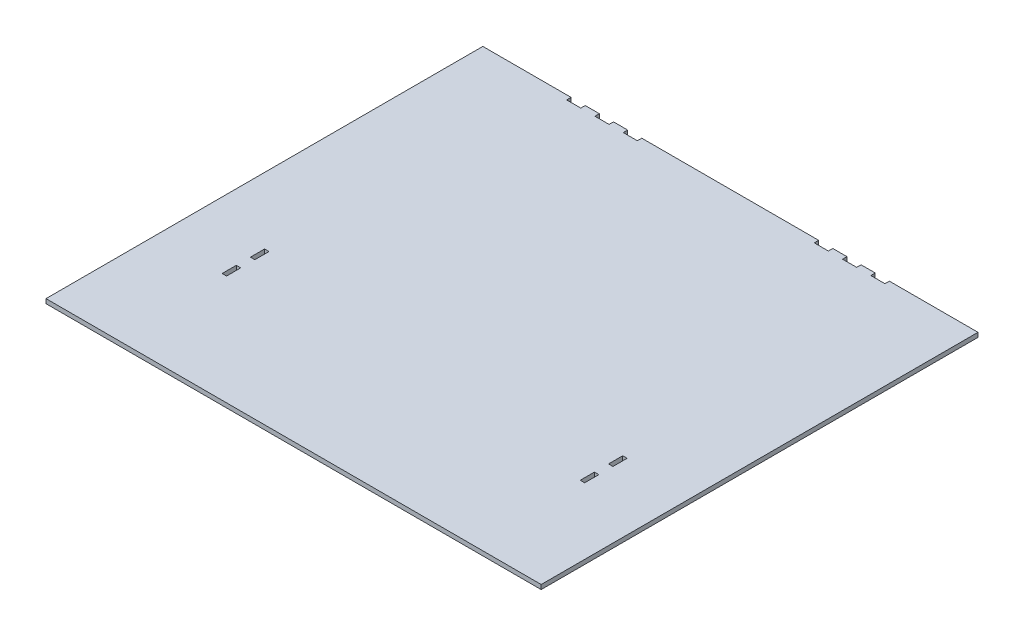
SolidWorks part; units mm, degrees
ref_plane "Front Plane" through (0, 0, 0) normal (0, 0, 1) x (1, 0, 0)
ref_plane "Top Plane" through (0, 0, 0) normal (0, 1, 0) x (1, 0, 0)
ref_plane "Right Plane" through (0, 0, 0) normal (1, 0, 0) x (0, 0, -1)
sketch "Sketch1" plane through (0, 0, 0) normal (0, 1, 0) x (1, 0, 0)
  line L1 (-280, 247) -> (-180.2136, 247)
  line L2 (-280, 247) -> (-280, -247)
  line L3 (-280, -247) -> (280, -247)
  line L4 (280, 247) -> (280, -247)
  line L5 (-280, 247) -> (280, -247) construction
  line L6 (-280, -247) -> (280, 247) construction
  line L8 (-200, -74.801) -> (-200, -90.8019)
  line L11 (-100.2136, 247) -> (99.7864, 247)
  line L12 (-100.2136, 242) -> (-116.2136, 242)
  line L14 (-180.2136, 242) -> (-180.2136, 247)
  line L20 (-100.2136, 242) -> (-100.2136, 247)
  line L21 (-132.2136, 242) -> (-148.2136, 242)
  line L23 (-132.2136, 247) -> (-116.2136, 247)
  line L29 (-164.2136, 242) -> (-180.2136, 242)
  line L30 (-164.2136, 242) -> (-164.2136, 247)
  line L31 (-148.2136, 242) -> (-148.2136, 247)
  line L32 (-132.2136, 242) -> (-132.2136, 247)
  line L33 (-116.2136, 242) -> (-116.2136, 247)
  line L34 (-164.2136, 247) -> (-148.2136, 247)
  line L35 (179.7864, 242) -> (179.7864, 247)
  line L36 (163.7864, 242) -> (179.7864, 242)
  line L37 (163.7864, 242) -> (163.7864, 247)
  line L39 (147.7864, 242) -> (147.7864, 247)
  line L40 (131.7864, 242) -> (147.7864, 242)
  line L41 (131.7864, 242) -> (131.7864, 247)
  line L43 (115.7864, 242) -> (115.7864, 247)
  line L44 (99.7864, 242) -> (115.7864, 242)
  line L45 (99.7864, 242) -> (99.7864, 247)
  line L46 (115.7864, 247) -> (131.7864, 247)
  line L47 (147.7864, 247) -> (163.7864, 247)
  line L48 (179.7864, 247) -> (280, 247)
  line L59 (205, -122.8038) -> (205, -106.8029)
  line L62 (205, -90.8019) -> (205, -74.801)
  line L65 (-205, -90.8019) -> (-205, -74.801)
  line L67 (-205, -122.8038) -> (-205, -106.8029)
  line L68 (-200, -106.8029) -> (-200, -122.8038)
  line L70 (200, -74.801) -> (200, -90.8019)
  line L72 (200, -106.8029) -> (200, -122.8038)
  line L74 (-200, -74.801) -> (-205, -74.801)
  line L75 (-200, -90.8019) -> (-205, -90.8019)
  line L76 (-200, -106.8029) -> (-205, -106.8029)
  line L77 (-200, -122.8038) -> (-205, -122.8038)
  line L78 (200, -74.801) -> (205, -74.801)
  line L79 (200, -90.8019) -> (205, -90.8019)
  line L80 (200, -106.8029) -> (205, -106.8029)
  line L81 (200, -122.8038) -> (205, -122.8038)
  point P0 (0, 0)
  dimension "D1" = 560
  dimension "D2" = 494
  dimension "D3" = 5
  dimension "D4" = 80
  dimension "D5" = 5
  dimension "D6" = 5
  dimension "D7" = 5
  dimension "D8" = 5
extrude "Boss-Extrude1" add sketch "Sketch1" along normal blind 5
